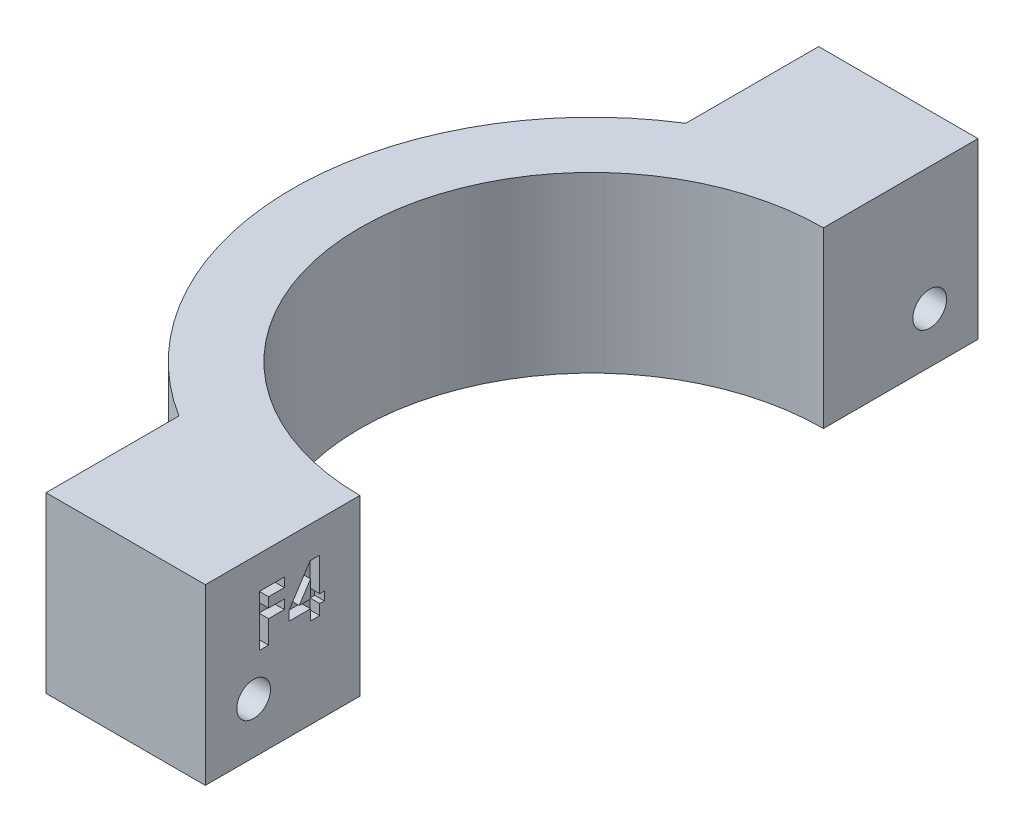
SolidWorks part; units mm, degrees
ref_plane "Front Plane" through (0, 0, 0) normal (0, 0, 1) x (1, 0, 0)
ref_plane "Top Plane" through (0, 0, 0) normal (0, 1, 0) x (1, 0, 0)
ref_plane "Right Plane" through (0, 0, 0) normal (1, 0, 0) x (0, 0, -1)
sketch "Sketch1" plane through (0, 0, 0) normal (0, 1, 0) x (1, 0, 0)
  line L0 (-46.9983, 32.5286) -> (-46.9983, -47.4714)
  line L1 (-46.9983, -47.4714) -> (-13.9983, -47.4714)
  line L2 (-13.9983, -47.4714) -> (-13.9983, -31.4714)
  line L3 (-46.9983, 32.5286) -> (-13.9983, 32.5286)
  line L4 (-13.9983, 32.5286) -> (-13.9983, 16.5286)
  line L5 (-30.4983, 32.5286) -> (-30.4983, 18.7726)
  line L6 (-30.4983, -33.7155) -> (-30.4983, -47.4714)
  arc A0 (-13.9983, 16.5286) -> (-13.9983, -31.4714) centre (-13.9983, -7.4714) ccw
  arc A1 (-13.9983, 23.5286) -> (-13.9983, -38.4714) centre (-13.9983, -7.4714) ccw
  dimension "D1" = 80
  dimension "D2" = 33
  dimension "D3" = 33
  dimension "D4" = 48
  dimension "D5" = 16
  dimension "D6" = 16
  dimension "D7" = 7
extrude "Boss-Extrude1" add sketch "Sketch1" along normal blind 18 contours A1 L4 L3 L5 | L4 A1 L2 A0 | A1 L6 L1 L2
sketch "Sketch2" plane through (-13.9983, 0, 0) normal (1, 0, 0) x (0, 0, -1)
  line L0 (-47.4714, 18) -> (-47.4714, 0) construction
  line L3 (32.5286, 18) -> (32.5286, 0) construction
  line L8 (32.5286, 18) -> (16.5286, 18) construction
  line L9 (-47.4714, 18) -> (-31.4714, 18) construction
  circle A0 centre (-42.4714, 5.25) radius 1.75
  circle A1 centre (27.5286, 5.25) radius 1.75
  dimension "D3" = 12.75
  dimension "D5" = 3.5
  dimension "D6" = 3.5
  dimension "D1" = 5
  dimension "D2" = 5
  dimension "D4" = 12.75
extrude "Cut-Extrude1" cut sketch "Sketch2" against normal through all
sketch "Sketch3" plane through (-13.9983, 0, 0) normal (1, 0, 0) x (0, 0, -1)
  text T0 "<b>F4</b>" font "Century Gothic" height in points 20
extrude "Cut-Extrude2" cut sketch "Sketch3" against normal blind 1
sketch "Sketch4" plane through (-30.4983, 0, 0) normal (-1, 0, 0) x (0, 0, 1)
  line L1 (-25.2188, 3.0709) -> (-24.4865, 6.1607)
  line L2 (-24.4865, 6.1607) -> (-26.7963, 8.3398)
  line L3 (-26.7963, 8.3398) -> (-29.8383, 7.4291)
  line L4 (-29.8383, 7.4291) -> (-30.5706, 4.3393)
  line L5 (-30.5706, 4.3393) -> (-28.2609, 2.1602)
  line L6 (-28.2609, 2.1602) -> (-25.2188, 3.0709)
  line L7 (44.3169, 2.6659) -> (45.6321, 5.5561)
  line L8 (45.6321, 5.5561) -> (43.7866, 8.1403)
  line L9 (43.7866, 8.1403) -> (40.626, 7.8341)
  line L10 (40.626, 7.8341) -> (39.3108, 4.9439)
  line L11 (39.3108, 4.9439) -> (41.1562, 2.3597)
  line L12 (41.1562, 2.3597) -> (44.3169, 2.6659)
  circle A0 centre (-27.5286, 5.25) radius 2.75 construction
  circle A1 centre (42.4714, 5.25) radius 2.75 construction
  point P10 (0, 0)
  dimension "D1" = 5.5
extrude "Cut-Extrude3" cut sketch "Sketch4" against normal blind 5
